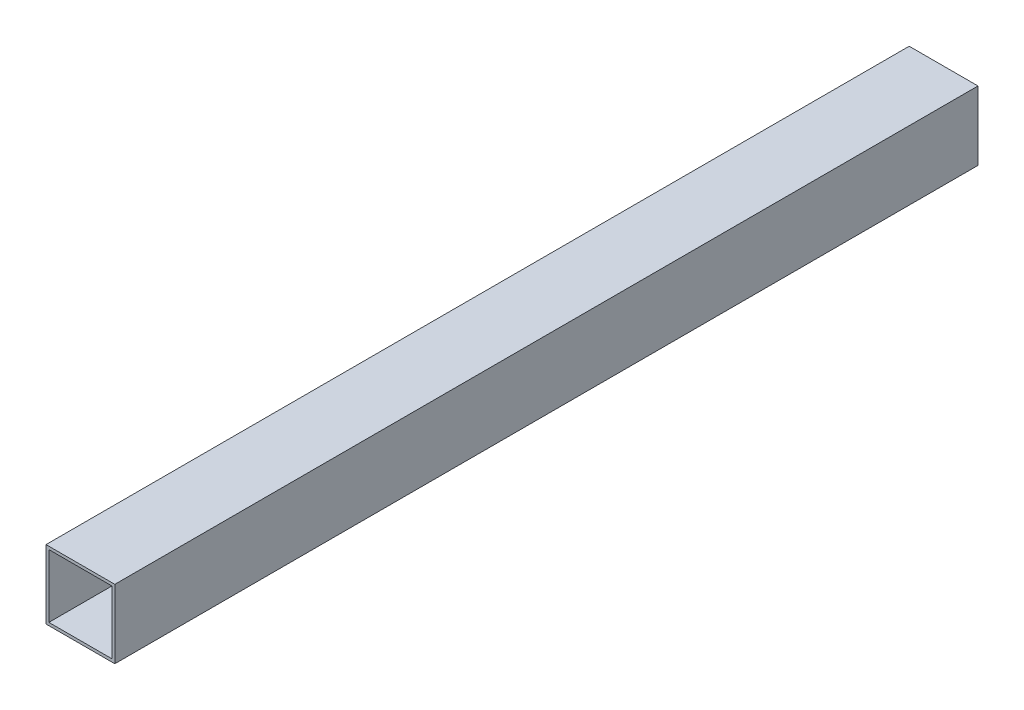
SolidWorks part; units mm, degrees
ref_plane "Front Plane" through (0, 0, 0) normal (0, 0, 1) x (1, 0, 0)
ref_plane "Top Plane" through (0, 0, 0) normal (0, 1, 0) x (1, 0, 0)
ref_plane "Right Plane" through (0, 0, 0) normal (1, 0, 0) x (0, 0, -1)
sketch "Sketch1" plane through (0, 0, 0) normal (0, 0, 1) x (1, 0, 0)
  line L5 (-33.401, 33.401) -> (33.401, 33.401)
  line L6 (-33.401, 33.401) -> (-33.401, -33.401)
  line L11 (-33.401, -33.401) -> (33.401, -33.401)
  line L12 (33.401, 33.401) -> (33.401, -33.401)
  line L13 (-33.401, 33.401) -> (33.401, -33.401) construction
  line L14 (-33.401, -33.401) -> (33.401, 33.401) construction
  line L15 (36.449, -36.449) -> (-36.449, -36.449)
  line L16 (36.449, -36.449) -> (36.449, 36.449)
  line L17 (36.449, 36.449) -> (-36.449, 36.449)
  line L18 (-36.449, -36.449) -> (-36.449, 36.449)
  line L19 (36.449, -36.449) -> (-36.449, 36.449) construction
  line L20 (36.449, 36.449) -> (-36.449, -36.449) construction
  point P0 (0, 0)
  point P6 (0, 0)
  dimension "D1" = 3.048
  dimension "D3" = 69.85
extrude "Boss-Extrude1" add sketch "Sketch1" along normal blind 914.4
